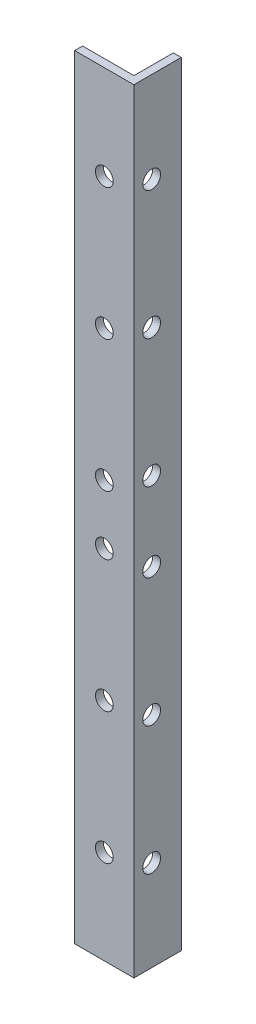
SolidWorks part; units mm, degrees
material "6061-T6 (SS)"
ref_plane "Alzado" through (0, 0, 0) normal (0, 0, 1) x (1, 0, 0)
ref_plane "Planta" through (0, 0, 0) normal (0, 1, 0) x (1, 0, 0)
ref_plane "Vista lateral" through (0, 0, 0) normal (1, 0, 0) x (0, 0, -1)
sketch "Sketch1" plane through (0, 0, 0) normal (0, 1, 0) x (1, 0, 0)
  line L0 (0, 0) -> (15, 0)
  line L1 (15, 0) -> (15, 12)
  line L2 (15, 12) -> (13, 12)
  line L3 (13, 12) -> (13, 2)
  line L4 (13, 2) -> (0, 2)
  line L5 (0, 2) -> (0, 0)
  dimension "D1" = 15
  dimension "D2" = 12
  dimension "D3" = 2
  dimension "D4" = 2
extrude "Boss-Extrude1" add sketch "Sketch1" along normal blind 196
sketch "Sketch4" plane through (0, 0, 0) normal (0, 0, 1) x (1, 0, 0)
  line L0 (15, 196) -> (15, 0) construction
  line L1 (0, 196) -> (15, 196)
  line L2 (0, 196) -> (0, 193)
  line L3 (0, 193) -> (15, 193)
  line L4 (15, 196) -> (15, 193)
  line L6 (0, 0) -> (15, 0)
  line L7 (0, 0) -> (0, 3)
  line L8 (0, 3) -> (15, 3)
  line L9 (15, 0) -> (15, 3)
  dimension "D1" = 3
  dimension "D2" = 3
extrude "Cut-Extrude3" [suppressed] cut sketch "Sketch4" against normal up to next
sketch "Sketch5" plane through (15, 0, 0) normal (1, 0, 0) x (0, 0, -1)
  circle A0 centre (4.5, 23) radius 2.25
  circle A1 centre (4.5, 55.5) radius 2.25
  circle A2 centre (4.5, 88) radius 2.25
  circle A3 centre (4.5, 108) radius 2.25
  circle A4 centre (4.5, 140.5) radius 2.25
  circle A5 centre (4.5, 173) radius 2.25
  dimension "D1" = 4.5
extrude "Cut-Extrude4" cut sketch "Sketch5" against normal up to next
sketch "Sketch6" plane through (0, 0, 0) normal (0, 0, 1) x (1, 0, 0)
  circle A0 centre (7.5, 23.8333) radius 2.25
  circle A1 centre (7.5, 57.1667) radius 2.25
  circle A2 centre (7.5, 90.5) radius 2.25
  circle A3 centre (7.5, 105.5) radius 2.25
  circle A4 centre (7.5, 138.8333) radius 2.25
  circle A5 centre (7.5, 172.1667) radius 2.25
  dimension "D1" = 4.5
extrude "Cut-Extrude5" cut sketch "Sketch6" against normal up to next
